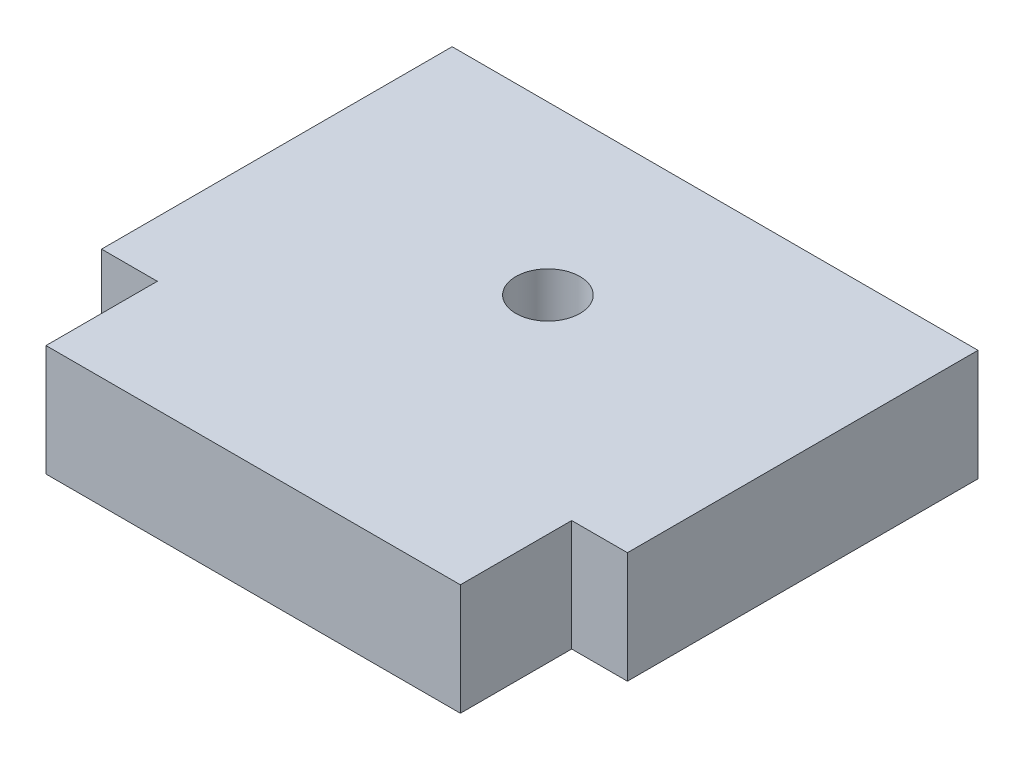
SolidWorks part; units mm, degrees
ref_plane "Front Plane" through (0, 0, 0) normal (0, 0, 1) x (1, 0, 0)
ref_plane "Top Plane" through (0, 0, 0) normal (0, 1, 0) x (1, 0, 0)
ref_plane "Right Plane" through (0, 0, 0) normal (1, 0, 0) x (0, 0, -1)
sketch "Sketch1" plane through (0, 0, 0) normal (0, 1, 0) x (1, 0, 0)
  line L0 (-15, -10) -> (-15, 10)
  line L1 (-15, -10) -> (-11.82, -10)
  line L2 (-15, 10) -> (15, 10)
  line L3 (15, -10) -> (15, 10)
  line L4 (-15, -10) -> (15, 10) construction
  line L5 (-15, 10) -> (15, -10) construction
  line L6 (-11.82, -16.35) -> (-11.82, -10)
  line L7 (-11.82, -16.35) -> (11.82, -16.35)
  line L9 (11.82, -16.35) -> (11.82, -10)
  line L10 (-11.82, -16.35) -> (11.82, -10) construction
  line L11 (-11.82, -10) -> (11.82, -16.35) construction
  line L12 (11.82, -10) -> (15, -10)
  point P1 (0, 0)
  point P2 (0, -13.175)
  dimension "D1" = 30
  dimension "D2" = 3.18
  dimension "D3" = 6.35
  dimension "D4" = 20
extrude "Boss-Extrude1" add sketch "Sketch1" along normal blind 6.35
sketch "Sketch2" plane through (0, 6.35, 0) normal (0, 1, 0) x (1, 0, 0)
  line L0 (11.82, -10) -> (15, -10) construction
  point P0 (0, 0.4648)
  dimension "D1" = 10.4648
hole_wizard "#6 Clearance Hole1" positions "Sketch4" profile "Sketch3" hole size "#6" standard "ANSI Inch" end condition through all
sketch "Sketch4" plane through (0, 6.35, 0) normal (0, 1, 0) x (1, 0, 0)
  point P0 (0, 0.4648)
sketch "Sketch3" plane through (0, 6.35, -0.4648) normal (1, 0, 0) x (0, 0, 1)
  line L0 (0, 0) -> (0, 6.35)
  line L1 (0, 6.35) -> (1.8288, 6.35)
  line L2 (1.8288, 6.35) -> (1.8288, 0)
  line L5 (1.8288, 0) -> (0, 0)
  line L11 (0, -6.35) -> (0, 107.95) construction
  dimension "Thru Hole Dia." = 3.6576
  dimension "Thru Hole Depth" = 6.35
